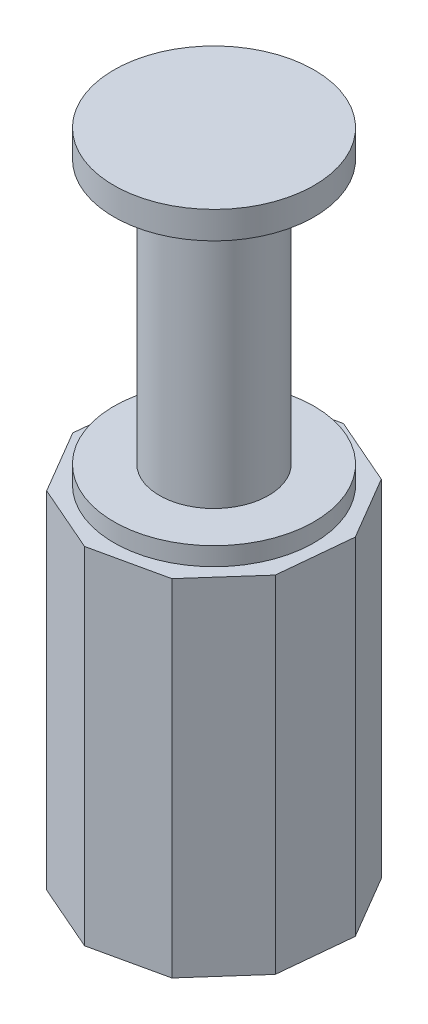
SolidWorks part; units mm, degrees
ref_plane "Спереди" through (0, 0, 0) normal (0, 0, 1) x (1, 0, 0)
ref_plane "Сверху" through (0, 0, 0) normal (0, 1, 0) x (1, 0, 0)
ref_plane "Справа" through (0, 0, 0) normal (1, 0, 0) x (0, 0, -1)
sketch "Эскиз2" plane through (0, 0, 0) normal (1, 0, 0) x (0, 0, -1)
  line L0 (0, -61.7012) -> (0, 99.8075) construction
  line L1 (0, 0) -> (55, 0)
  line L2 (55, 0) -> (55, 10)
  line L3 (55, 10) -> (30, 10)
  line L4 (30, 10) -> (30, 155)
  line L5 (30, 155) -> (55, 155)
  line L6 (55, 155) -> (55, 170)
  line L7 (55, 170) -> (0, 170)
  line L8 (0, 0) -> (0, 170)
revolve "Повернуть1" add sketch "Эскиз2" angle 360 about L0
sketch "Эскиз3" plane through (0, 0, 0) normal (0, -1, 0) x (1, 0, 0)
  line L0 (43.1931, -48.7181) -> (63.5797, -14.0255)
  line L1 (-6.3082, 64.802) -> (-43.1931, 48.7181)
  line L2 (-43.1931, 48.7181) -> (-63.5797, 14.0255)
  line L3 (-63.5797, 14.0255) -> (-59.6811, -26.0243)
  line L4 (-59.6811, -26.0243) -> (-32.9863, -56.1338)
  line L5 (-32.9863, -56.1338) -> (6.3082, -64.802)
  line L6 (6.3082, -64.802) -> (43.1931, -48.7181)
  line L7 (63.5797, -14.0255) -> (59.6811, 26.0243)
  line L8 (59.6811, 26.0243) -> (32.9863, 56.1338)
  line L9 (32.9863, 56.1338) -> (-6.3082, 64.802)
  circle A0 centre (0, 0) radius 61.9217 construction
extrude "Бобышка-Вытянуть2" add sketch "Эскиз3" along normal blind 190
